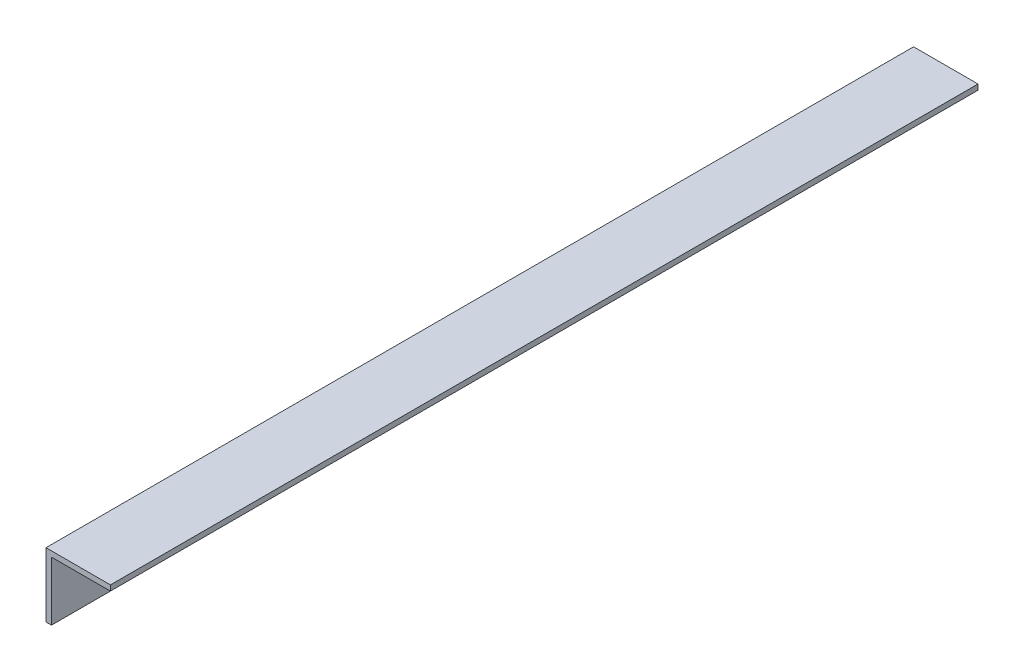
SolidWorks part; units mm, degrees
material "6061-T6 (SS)"
ref_plane "Front Plane" through (0, 0, 0) normal (0, 0, 1) x (1, 0, 0)
ref_plane "Top Plane" through (0, 0, 0) normal (0, 1, 0) x (1, 0, 0)
ref_plane "Right Plane" through (0, 0, 0) normal (1, 0, 0) x (0, 0, -1)
sketch "Sketch1" plane through (0, 0, 0) normal (0, 0, 1) x (1, 0, 0)
  line L0 (0, 0) -> (-19.05, 0)
  line L1 (-19.05, 0) -> (-19.05, -19.05)
  line L2 (-19.05, -19.05) -> (-17.4498, -19.05)
  line L3 (-17.4498, -19.05) -> (-17.4498, -1.6002)
  line L4 (-17.4498, -1.6002) -> (0, -1.6002)
  line L5 (0, -1.6002) -> (0, 0)
  dimension "D1" = 1.6002
  dimension "D2" = 19.05
extrude "Boss-Extrude1" add sketch "Sketch1" along normal blind 256.54
